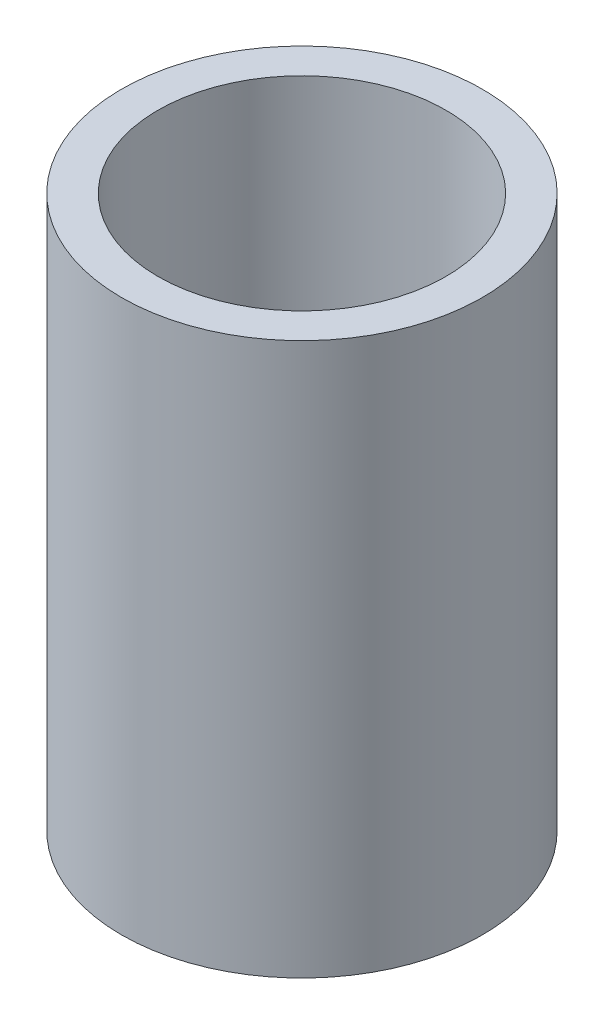
SolidWorks part; units mm, degrees
ref_plane "Front Plane" through (0, 0, 0) normal (0, 0, 1) x (1, 0, 0)
ref_plane "Top Plane" through (0, 0, 0) normal (0, 1, 0) x (1, 0, 0)
ref_plane "Right Plane" through (0, 0, 0) normal (1, 0, 0) x (0, 0, -1)
sketch "Sketch1" plane through (0, 0, 0) normal (0, 1, 0) x (1, 0, 0)
  circle A0 centre (0, 0) radius 13.4938
  circle A1 centre (0, 0) radius 10.7696
  dimension "D1" = 26.9875
  dimension "D2" = 21.5392
extrude "Boss-Extrude2" add sketch "Sketch1" along normal mid plane 41.275
sketch "Sketch4" plane through (0, 0, 0) normal (0, 1, 0) x (1, 0, 0)
  circle A0 centre (0, 0) radius 10.7696
  circle A1 centre (0, 0) radius 8.001
  dimension "D1" = 2.7686
  dimension "D2" = 21.5392
extrude "Boss-Extrude4" add sketch "Sketch4" along normal mid plane 1.5875
